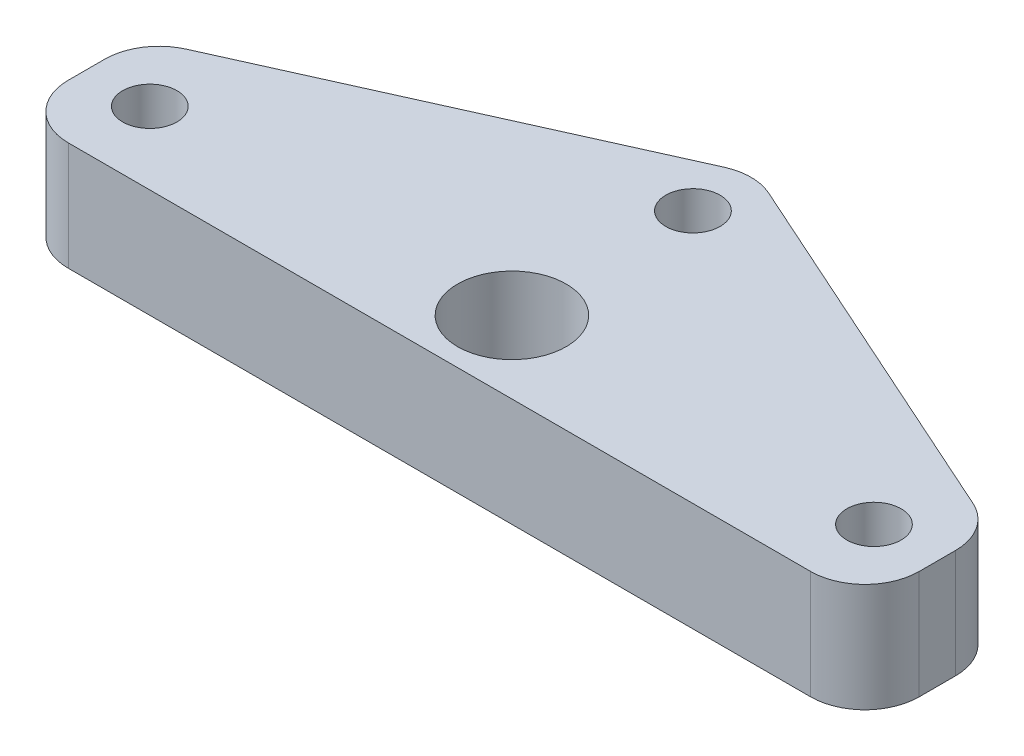
SolidWorks part; units mm, degrees
ref_plane "Front Plane" through (0, 0, 0) normal (0, 0, 1) x (1, 0, 0)
ref_plane "Top Plane" through (0, 0, 0) normal (0, 1, 0) x (1, 0, 0)
ref_plane "Right Plane" through (0, 0, 0) normal (1, 0, 0) x (0, 0, -1)
sketch "Sketch1" plane through (0, 0, 0) normal (0, 1, 0) x (1, 0, 0)
  line L0 (23.5, 0) -> (-23.5, 0)
  line L1 (-23.5, 0) -> (-23.5, 6.946)
  line L2 (-23.5, 6.946) -> (0, 17.5)
  line L3 (0, 17.5) -> (23.5, 6.946)
  line L4 (23.5, 6.946) -> (23.5, 0)
  line L5 (0, 0) -> (0, 28.2528) construction
  circle A0 centre (0, 4) radius 3
  circle A1 centre (20, 4) radius 1.5
  circle A2 centre (-20, 4) radius 1.5
  circle A3 centre (0, 14) radius 1.5
  point P3 (0, 0)
  point P15 (0, 0)
  point P16 (0, 0)
  dimension "D1" = 47
  dimension "D3" = 6
  dimension "D7" = 3
  dimension "D2" = 4
  dimension "D4" = 40
  dimension "D5" = 10
  dimension "D6" = 3.5
extrude "Boss-Extrude1" add sketch "Sketch1" along normal blind 6
fillet "Fillet1" radius 3 5 edges at (-23.5, 3, 0) (-23.5, 3, -6.946) (0, 3, -17.5) (23.5, 3, -6.946) (23.5, 3, 0)
